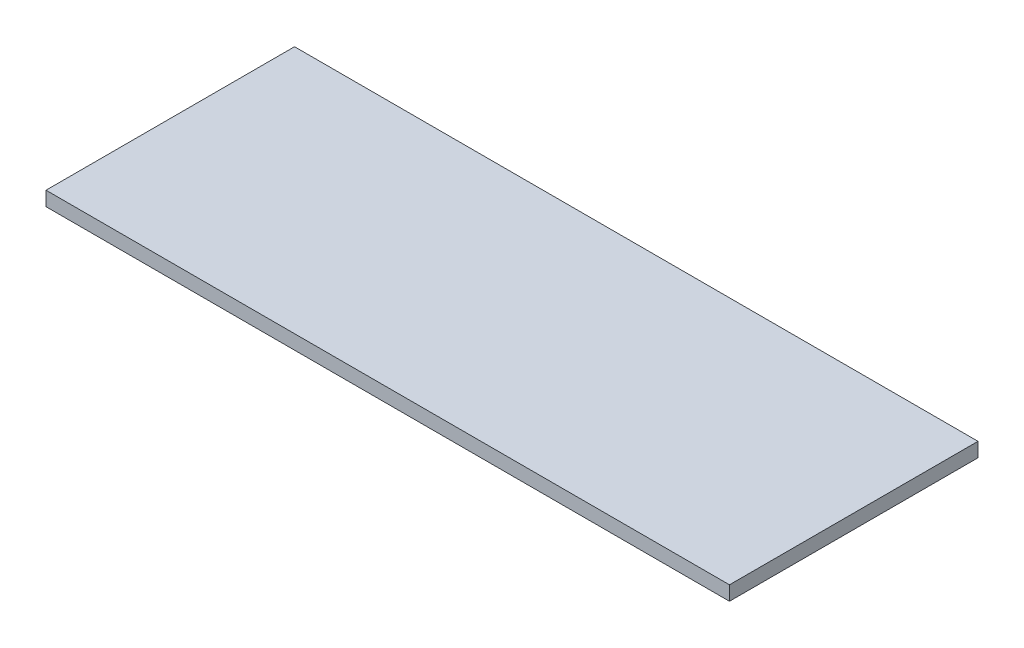
SolidWorks part; units mm, degrees
ref_plane "Plane1" through (0, 0, 0) normal (0, 0, 1) x (1, 0, 0)
ref_plane "Plane2" through (0, 0, 0) normal (0, 1, 0) x (1, 0, 0)
ref_plane "Plane3" through (0, 0, 0) normal (1, 0, 0) x (0, 0, -1)
sketch "Sketch1" plane through (0, 0, 0) normal (0, 1, 0) x (1, 0, 0)
  line L1 (0, 0) -> (-55, 0)
  line L2 (0, 0) -> (0, 20)
  line L3 (0, 20) -> (-55, 20)
  line L4 (-55, 0) -> (-55, 20)
  dimension "D1" = 20
  dimension "D2" = 55
extrude "Boss-Extrude1" add sketch "Sketch1" along normal blind 1.15
